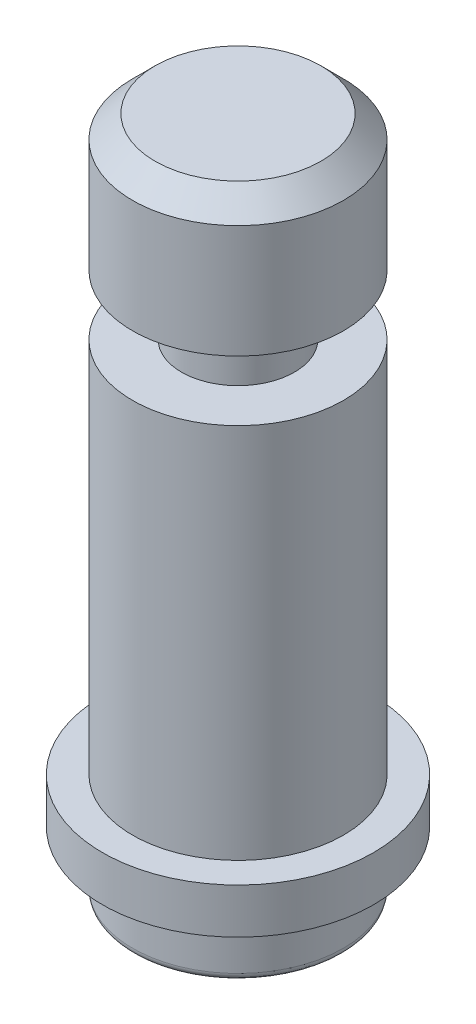
SolidWorks part; units mm, degrees
ref_plane "Alzado" through (0, 0, 0) normal (0, 0, 1) x (1, 0, 0)
ref_plane "Planta" through (0, 0, 0) normal (0, 1, 0) x (1, 0, 0)
ref_plane "Vista lateral" through (0, 0, 0) normal (1, 0, 0) x (0, 0, -1)
sketch "Croquis1" plane through (0, 0, 0) normal (0, 0, 1) x (1, 0, 0)
  line L0 (0, 22.5) -> (0, -22.5) construction
  line L1 (0, -22.5) -> (7, -22.5)
  line L2 (7, -22.5) -> (7, -18.5)
  line L3 (7, -18.5) -> (9, -18.5)
  line L4 (9, -18.5) -> (9, -15.5)
  line L5 (9, -15.5) -> (7, -15.5)
  line L6 (7, -15.5) -> (7, 9.5)
  line L7 (7, 9.5) -> (3.75, 9.5)
  line L8 (3.75, 9.5) -> (3.75, 13.5)
  line L9 (3.75, 13.5) -> (7, 13.5)
  line L10 (7, 13.5) -> (7, 22.5)
  line L11 (7, 22.5) -> (0, 22.5)
  line L12 (0, 22.5) -> (0, -22.5)
  dimension "D1" = 45
  dimension "D2" = 7
  dimension "D3" = 7.5
  dimension "D4" = 18
  dimension "D5" = 4
  dimension "D6" = 3
  dimension "D7" = 25
  dimension "D8" = 9
revolve "Revolución1" add sketch "Croquis1" angle 360 about L0
chamfer "Chaflán1" distance 1.5 angle 45 1 edges at (-7, 22.5, 0)
fillet "Redondeo1" radius 0.5 1 edges at (-7, -22.5, 0)
